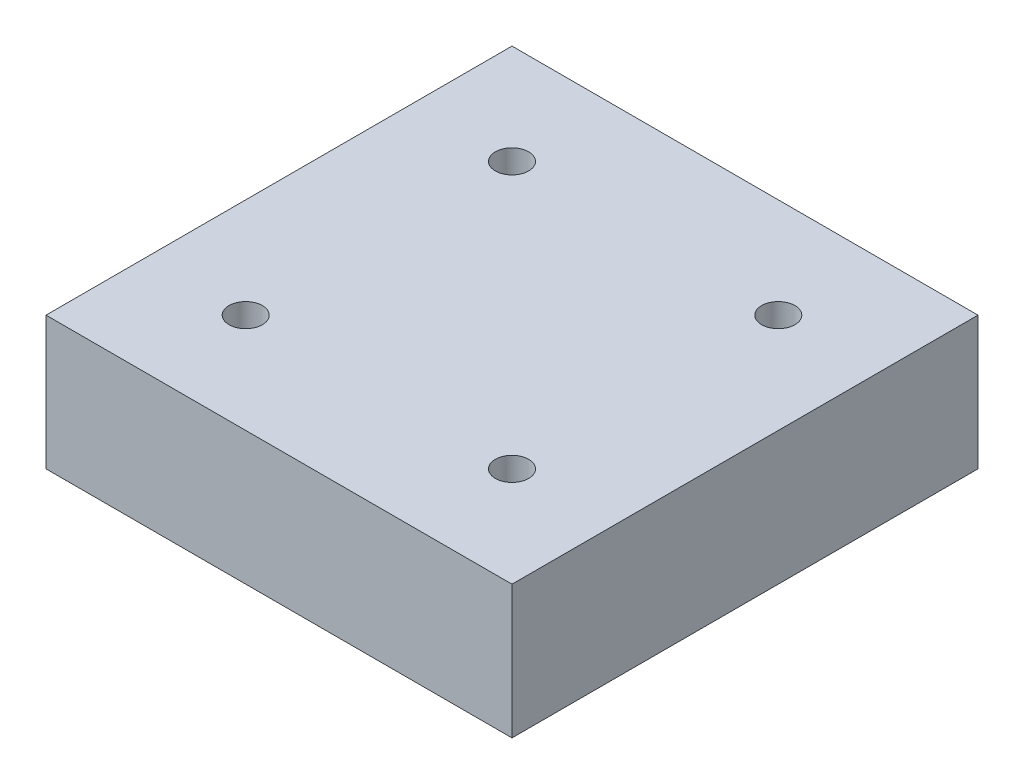
SolidWorks part; units mm, degrees
material "AISI 304"
ref_plane "前视基准面" through (0, 0, 0) normal (0, 0, 1) x (1, 0, 0)
ref_plane "上视基准面" through (0, 0, 0) normal (0, 1, 0) x (1, 0, 0)
ref_plane "右视基准面" through (0, 0, 0) normal (1, 0, 0) x (0, 0, -1)
sketch "Sketch1" plane through (0, 0, 0) normal (0, 1, 0) x (1, 0, 0)
  line L1 (-35, -35) -> (35, -35)
  line L2 (-35, -35) -> (-35, 35)
  line L3 (-35, 35) -> (35, 35)
  line L4 (35, -35) -> (35, 35)
  line L5 (-35, -35) -> (35, 35) construction
  line L6 (-35, 35) -> (35, -35) construction
  point P0 (0, 0)
  dimension "D1" = 70
extrude "Boss-Extrude1" add sketch "Sketch1" along normal blind 20
hole_wizard "M6 Tapped Hole1" positions "Sketch2" profile "Sketch3" tap size "M6" standard "GB"
sketch "Sketch2" plane through (0, 20, 0) normal (0, 1, 0) x (1, 0, 0)
  line L0 (-11, 0) -> (11, 0) construction
  line L1 (0, -11) -> (0, 11) construction
  point P0 (20, 20)
  point P6 (20, -20)
  point P9 (-20, -20)
  point P10 (-20, 20)
  dimension "D1" = 20
  dimension "D2" = 20
sketch "Sketch3" plane through (20, 20, -20) normal (1, 0, 0) x (0, 0, 1)
  line L0 (0, 0) -> (0, 16.5022)
  line L1 (0, 16.5022) -> (2.5, 15)
  line L2 (2.5, 15) -> (2.5, 0)
  line L5 (2.5, 0) -> (0, 0)
  line L10 (0, 16.5022) -> (-2.5, 15) construction
  line L11 (0, -6.35) -> (0, 107.95) construction
  dimension "Tap Drill Dia." = 5
  dimension "Tap Drill Depth" = 15
  dimension "Drill Angle" = 118
cosmetic thread "Hole Thread1" parameters "D1"=12, "D2"=6
cosmetic thread "Hole Thread2" parameters "D1"=12, "D2"=6
cosmetic thread "Hole Thread3" parameters "D1"=12, "D2"=6
cosmetic thread "Hole Thread4" parameters "D1"=12, "D2"=6
